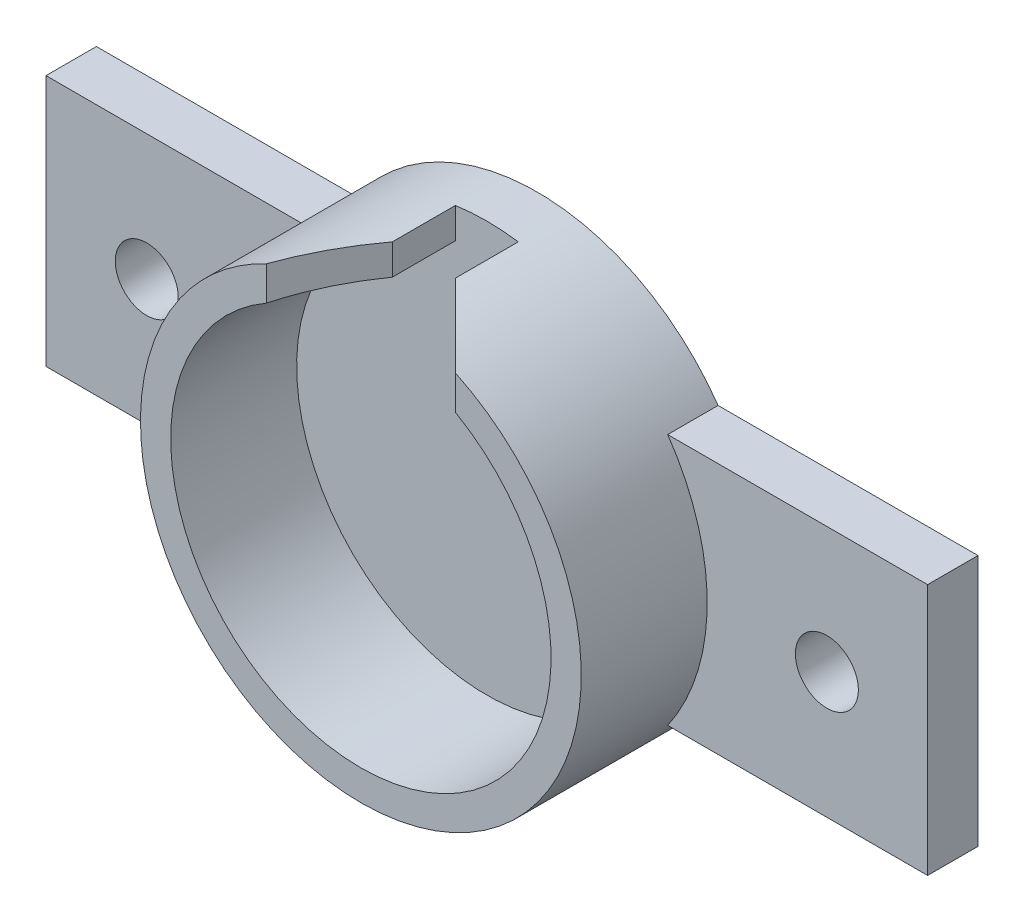
SolidWorks part; units mm, degrees
ref_plane "Front Plane" through (0, 0, 0) normal (0, 0, 1) x (1, 0, 0)
ref_plane "Top Plane" through (0, 0, 0) normal (0, 1, 0) x (1, 0, 0)
ref_plane "Right Plane" through (0, 0, 0) normal (1, 0, 0) x (0, 0, -1)
sketch "Sketch1" plane through (0, 0, 0) normal (0, 0, 1) x (1, 0, 0)
  circle A0 centre (0, 0) radius 15.1
  circle A1 centre (0, 0) radius 17.5
  dimension "D1" = 30.2
extrude "Boss-Extrude1" add sketch "Sketch1" along normal blind 10
sketch "Sketch2" plane through (0, 0, 0) normal (0, 0, -1) x (-1, 0, 0)
  line L0 (14.3614, 10) -> (35, 10)
  line L1 (-35, 10) -> (-14.3614, 10)
  line L2 (-35, 10) -> (-35, -10)
  line L3 (-35, -10) -> (-14.3614, -10)
  line L4 (35, 10) -> (35, -10)
  line L5 (-35, 10) -> (35, -10) construction
  line L6 (-35, -10) -> (35, 10) construction
  line L7 (14.3614, -10) -> (35, -10)
  arc A0 (-14.3614, -10) -> (14.3614, -10) centre (0, 0) ccw
  arc A1 (14.3614, 10) -> (-14.3614, 10) centre (0, 0) ccw
  point P0 (0, 0)
  dimension "D1" = 20
  dimension "D2" = 70
extrude "Boss-Extrude2" add sketch "Sketch2" along normal blind 4
sketch "Sketch3" plane through (0, 0, 0) normal (0, 0, 1) x (1, 0, 0)
  line L0 (-35, 0) -> (-27, 0) construction
  line L1 (-35, -10) -> (-35, 10) construction
  line L2 (0, -7.7) -> (0, 7.7) construction
  circle A0 centre (-27, 0) radius 2.5
  circle A1 centre (27, 0) radius 2.5
  dimension "D1" = 8
extrude "Cut-Extrude1" cut sketch "Sketch3" against normal blind 4
sketch "Sketch4" plane through (0, 0, 10) normal (0, 0, 1) x (1, 0, 0)
  line L0 (0, 0) -> (0, 15.1) construction
  line L2 (-2.5, 19.1) -> (2.5, 19.1)
  line L3 (-2.5, 19.1) -> (-2.5, 11.1)
  line L4 (-2.5, 11.1) -> (2.5, 11.1)
  line L5 (2.5, 19.1) -> (2.5, 11.1)
  line L6 (-2.5, 19.1) -> (2.5, 11.1) construction
  line L7 (-2.5, 11.1) -> (2.5, 19.1) construction
  circle A0 centre (0, 0) radius 15.1 construction
  dimension "D1" = 5
  dimension "D2" = 8
extrude "Cut-Extrude2" cut sketch "Sketch4" against normal blind 10
chamfer "Chamfer1" distance 5 angle 45 2 edges at (-2.5, 16.1061, 10) (2.5, 16.1061, 10)
